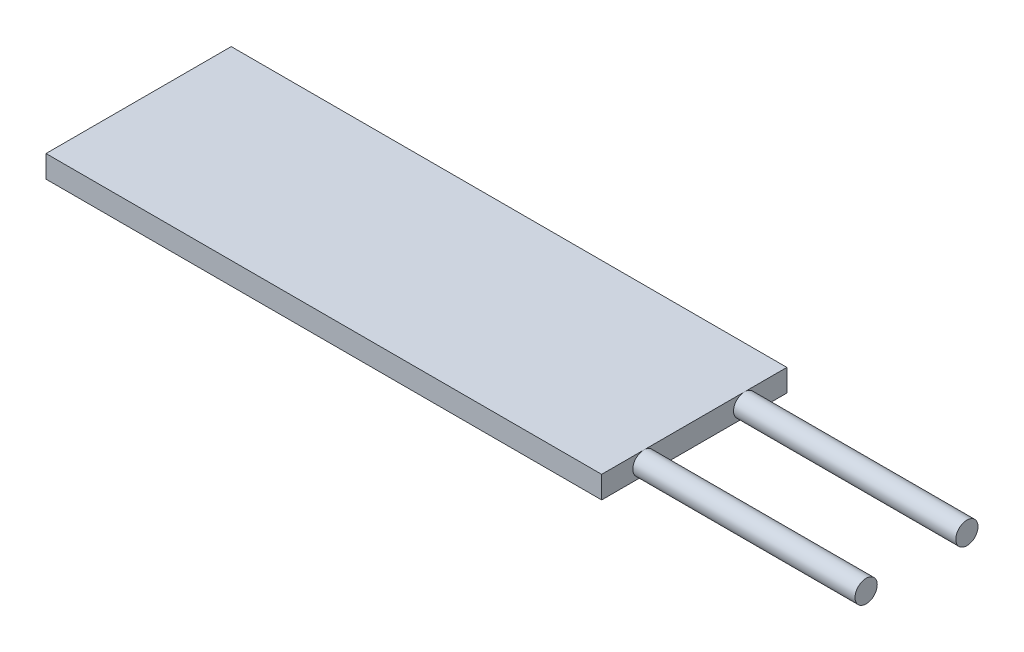
SolidWorks part; units mm, degrees
ref_plane "Front Plane" through (0, 0, 0) normal (0, 0, 1) x (1, 0, 0)
ref_plane "Top Plane" through (0, 0, 0) normal (0, 1, 0) x (1, 0, 0)
ref_plane "Right Plane" through (0, 0, 0) normal (1, 0, 0) x (0, 0, -1)
sketch "Sketch1" plane through (0, 0, 0) normal (1, 0, 0) x (0, 0, -1)
  line L1 (-12.5, -1.5) -> (12.5, -1.5)
  line L2 (-12.5, -1.5) -> (-12.5, 1.5)
  line L3 (-12.5, 1.5) -> (12.5, 1.5)
  line L4 (12.5, -1.5) -> (12.5, 1.5)
  line L5 (-12.5, -1.5) -> (12.5, 1.5) construction
  line L6 (-12.5, 1.5) -> (12.5, -1.5) construction
  point P0 (0, 0)
  dimension "D1" = 3
  dimension "D2" = 25
extrude "Boss-Extrude1" add sketch "Sketch1" along normal blind 75
sketch "Sketch2" plane through (75, 0, 0) normal (1, 0, 0) x (0, 0, -1)
  line L0 (0, 1.5) -> (0, -1.5) construction
  line L1 (12.5, 1.5) -> (-12.5, 1.5) construction
  line L2 (-12.5, -1.5) -> (12.5, -1.5) construction
  circle A0 centre (-6.8, 0) radius 1.5
  circle A1 centre (6.8, 0) radius 1.5
  dimension "D1" = 6.8
extrude "Boss-Extrude2" add sketch "Sketch2" along normal blind 30
